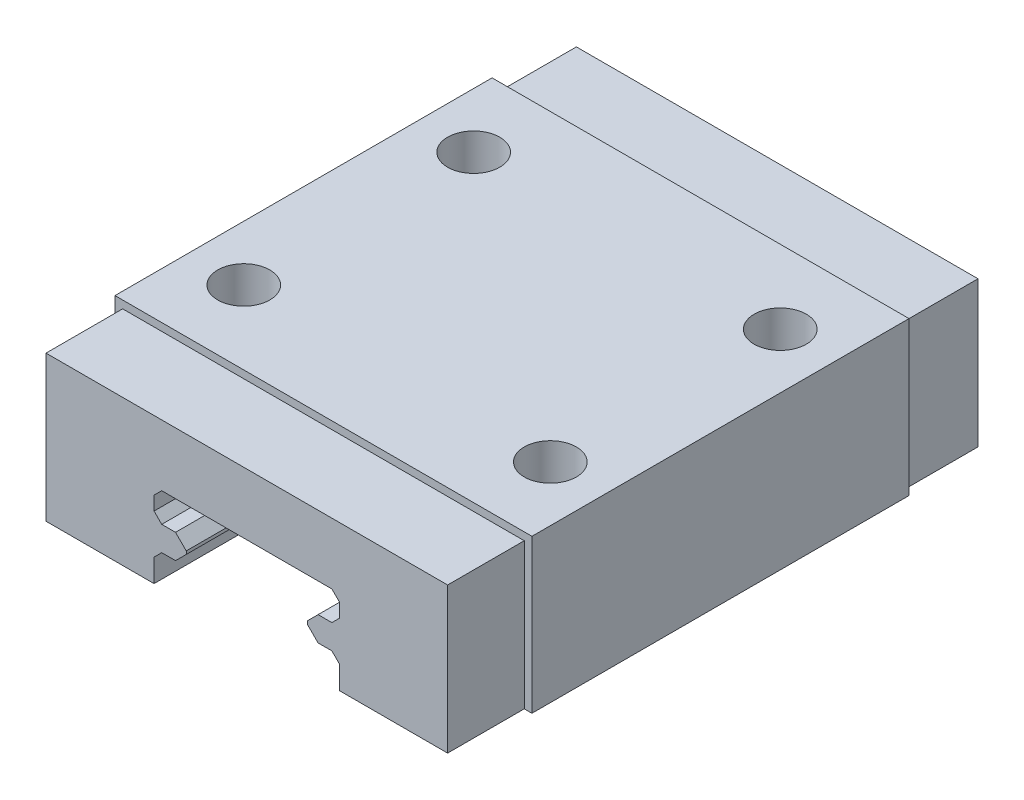
SolidWorks part; units mm, degrees
ref_plane "Front Plane" through (0, 0, 0) normal (0, 0, 1) x (1, 0, 0)
ref_plane "Top Plane" through (0, 0, 0) normal (0, 1, 0) x (1, 0, 0)
ref_plane "Right Plane" through (0, 0, 0) normal (1, 0, 0) x (0, 0, -1)
sketch "Sketch1" plane through (0, 0, 0) normal (0, 0, 1) x (1, 0, 0)
  line L1 (-13.6, 5) -> (13.6, 5)
  line L2 (-13.6, 5) -> (-13.6, -5)
  line L3 (-13.6, -5) -> (13.6, -5)
  line L4 (13.6, 5) -> (13.6, -5)
  line L5 (-13.6, 5) -> (13.6, -5) construction
  line L6 (-13.6, -5) -> (13.6, 5) construction
  point P0 (0, 0)
  dimension "D1" = 10
  dimension "D2" = 27.2
extrude "Boss-Extrude1" add sketch "Sketch1" along normal blind 34.6
sketch "Sketch2" plane through (0, 0, 34.6) normal (0, 0, 1) x (1, 0, 0)
  line L0 (-6.05, -3.5) -> (-6.05, -7)
  line L4 (6.05, -7) -> (6.05, -3.5)
  line L5 (6.05, -3.5) -> (5.55, -3)
  line L6 (5.55, -3) -> (3.95, -3)
  line L7 (3.95, -3) -> (3.95, -1.4)
  line L8 (3.95, -1.4) -> (5.55, -1.4)
  line L9 (5.55, -1.4) -> (6.05, -0.9)
  line L10 (6.05, -0.9) -> (6.05, 0)
  line L11 (6.05, 0) -> (5.55, 0.5)
  line L12 (5.55, 0.5) -> (-5.55, 0.5)
  line L13 (-5.55, 0.5) -> (-6.05, 0)
  line L14 (-6.05, 0) -> (-6.05, -0.9)
  line L15 (-6.05, -0.9) -> (-5.55, -1.4)
  line L16 (-5.55, -1.4) -> (-3.95, -1.4)
  line L17 (-3.95, -1.4) -> (-3.95, -3)
  line L18 (-3.95, -3) -> (-5.55, -3)
  line L19 (-5.55, -3) -> (-6.05, -3.5)
  line L20 (-13.6, -5) -> (13.6, -5) construction
  point P2 (0, 0.5)
  line M24 (-13.6, -5) -> (13.6, -5)
  dimension "D1" = 5.5
extrude "Cut-Extrude1" cut sketch "Sketch2" against normal blind 34.6 and the other way through all contours L18 L19 L0 L4 L5 L6 L7 L8 L9 L10 L11 L12 L13 L14 L15 L16 L17 M24
chamfer "Chamfer1" distance 0.7 angle 45 4 edges at (-3.95, -3, 17.3) (-3.95, -1.4, 17.3) (3.95, -3, 17.3) (3.95, -1.4, 17.3)
sketch "Sketch5" plane through (0, 5, 0) normal (0, 1, 0) x (1, 0, 0)
  point P0 (0, -17.3)
hole_wizard "M3 Clearance Hole1" positions "Sketch3" profile "Sketch4" hole size "M3" standard "ISO"
sketch "Sketch3" plane through (0, 5, 0) normal (0, 1, 0) x (1, 0, 0)
  point P0 (-10, -24.8)
  point P2 (-10, -9.8)
  point P4 (10, -9.8)
  point P6 (10, -24.8)
  dimension "D1" = 7.5
  dimension "D2" = 7.5
  dimension "D3" = 7.5
  dimension "D4" = 7.5
  dimension "D5" = 10
  dimension "D6" = 10
  dimension "D7" = 10
  dimension "D8" = 10
sketch "Sketch4" plane through (-10, 5, 24.8) normal (1, 0, 0) x (0, 0, 1)
  line L0 (0, 0) -> (0, 6.0215)
  line L1 (0, 6.0215) -> (1.7, 5)
  line L2 (1.7, 5) -> (1.7, 0)
  line L5 (1.7, 0) -> (0, 0)
  line L10 (0, 6.0215) -> (-1.7, 5) construction
  line L11 (0, -6.35) -> (0, 107.95) construction
  dimension "Hole Dia." = 3.4
  dimension "Hole Depth" = 5
  dimension "Drill Angle" = 118
sketch "Sketch6" plane through (0, 5, 0) normal (0, 1, 0) x (1, 0, 0)
  circle A0 centre (10, -24.8) radius 1.7 construction
  circle A1 centre (10, -9.8) radius 1.7 construction
  circle A2 centre (-10, -9.8) radius 1.7 construction
  circle A3 centre (-10, -24.8) radius 1.7 construction
  circle A4 centre (10, -24.8) radius 1.7
  circle A5 centre (10, -9.8) radius 1.7
  circle A6 centre (-10, -9.8) radius 1.7
  circle A7 centre (-10, -24.8) radius 1.7
  point P16 (0, -17.3)
sketch "Sketch7" plane through (0, 5, 0) normal (0, 1, 0) x (1, 0, 0)
  line L0 (-13.6, -29.6) -> (13.6, -29.6)
  line L1 (-13.6, -34.6) -> (-13.6, 0) construction
  line L2 (13.6, -34.6) -> (13.6, 0) construction
  line L3 (13.6, -34.6) -> (-13.6, -34.6) construction
  line L4 (-13.6, -5) -> (13.6, -5)
  line L5 (13.6, 0) -> (-13.6, 0) construction
  line L10 (13.6, 0) -> (-13.6, 0)
  line L11 (-13.6, 0) -> (-13.6, -34.6)
  line L12 (-13.6, -34.6) -> (13.6, -34.6)
  line L13 (13.6, -34.6) -> (13.6, 0)
  line L14 (13.6, 0) -> (-13.6, 0)
  line L15 (-13.6, 0) -> (-13.6, -34.6)
  line L16 (-13.6, -34.6) -> (13.6, -34.6)
  line L17 (13.6, -34.6) -> (13.6, 0)
  line M11 (13.6, 0) -> (-13.6, 0)
  line M12 (-13.6, 0) -> (-13.6, -34.6)
  line M13 (-13.6, -34.6) -> (13.6, -34.6)
  line M14 (13.6, -34.6) -> (13.6, 0)
  dimension "D1" = 5
  dimension "D2" = 5
  dimension "D3" = 0
extrude "Cut-Extrude2" cut sketch "Sketch7" against normal blind 0.5 contours L0 M12 M13 M14 | L4 M12 M14 M11
sketch "Sketch8" plane through (13.6, 0, 0) normal (1, 0, 0) x (0, 0, -1)
  line L0 (-29.6, 4.5) -> (-29.6, -5)
  line L1 (-34.6, -5) -> (0, -5) construction
  line L2 (-5, 4.5) -> (-5, -5)
  line L11 (-29.6, 5) -> (-29.6, 4.5)
  line L12 (-29.6, 4.5) -> (-34.6, 4.5)
  line L13 (-34.6, 4.5) -> (-34.6, -5)
  line L14 (-34.6, -5) -> (0, -5)
  line L15 (0, -5) -> (0, 4.5)
  line L16 (0, 4.5) -> (-5, 4.5)
  line L17 (-5, 4.5) -> (-5, 5)
  line L18 (-5, 5) -> (-29.6, 5)
  line L19 (-29.6, 5) -> (-29.6, 4.5)
  line L20 (-29.6, 4.5) -> (-34.6, 4.5)
  line L21 (-34.6, 4.5) -> (-34.6, -5)
  line L22 (-34.6, -5) -> (0, -5)
  line L23 (0, -5) -> (0, 4.5)
  line L24 (0, 4.5) -> (-5, 4.5)
  line L25 (-5, 4.5) -> (-5, 5)
  line L26 (-5, 5) -> (-29.6, 5)
  line M10 (-29.6, 4.5) -> (-34.6, 4.5)
  line M11 (-34.6, 4.5) -> (-34.6, -5)
  line M12 (-34.6, -5) -> (0, -5)
  line M13 (0, -5) -> (0, 4.5)
  line M14 (0, 4.5) -> (-5, 4.5)
  dimension "D1" = 0
extrude "Cut-Extrude3" cut sketch "Sketch8" against normal blind 0.5 contours L0 M10 M11 M12 | L2 M14 M12 M13
mirror "Mirror1" about plane through (0, 0, 0) normal (1, 0, 0) of "Cut-Extrude3"
